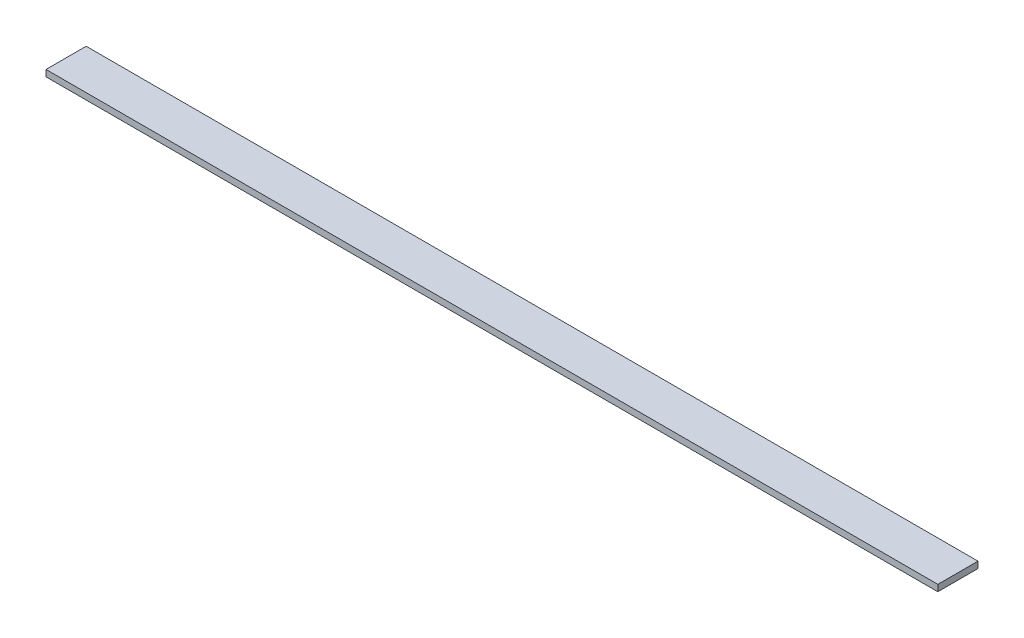
SolidWorks part; units mm, degrees
ref_plane "前视基准面" through (0, 0, 0) normal (0, 0, 1) x (1, 0, 0)
ref_plane "上视基准面" through (0, 0, 0) normal (0, 1, 0) x (1, 0, 0)
ref_plane "右视基准面" through (0, 0, 0) normal (1, 0, 0) x (0, 0, -1)
sketch "草图1" plane through (0, 0, 0) normal (0, 1, 0) x (1, 0, 0)
  line L1 (-277.5, -12.5) -> (277.5, -12.5)
  line L2 (-277.5, -12.5) -> (-277.5, 12.5)
  line L3 (-277.5, 12.5) -> (277.5, 12.5)
  line L4 (277.5, -12.5) -> (277.5, 12.5)
  line L5 (-277.5, -12.5) -> (277.5, 12.5) construction
  line L6 (-277.5, 12.5) -> (277.5, -12.5) construction
  point P0 (0, 0)
  dimension "D1" = 555
  dimension "D2" = 25
extrude "凸台-拉伸1" add sketch "草图1" along normal blind 4
